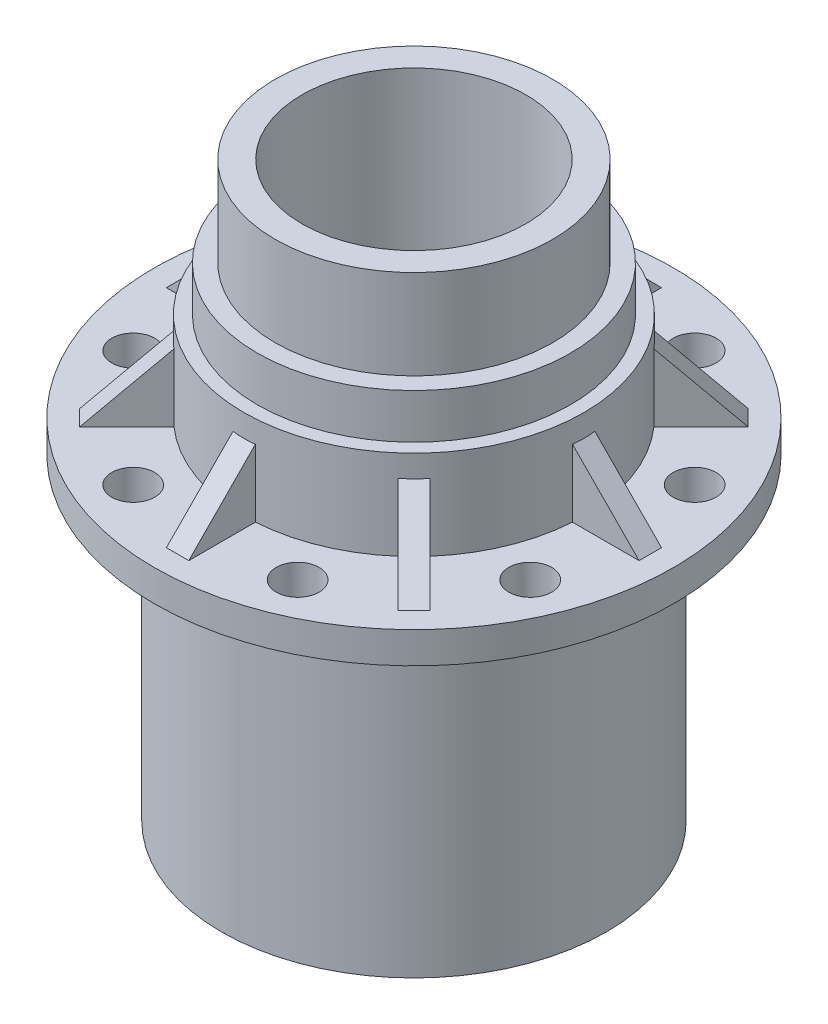
SolidWorks part; units mm, degrees
material "Plain Carbon Steel"
ref_plane "Front Plane" through (0, 0, 0) normal (0, 0, 1) x (1, 0, 0)
ref_plane "Top Plane" through (0, 0, 0) normal (0, 1, 0) x (1, 0, 0)
ref_plane "Right Plane" through (0, 0, 0) normal (1, 0, 0) x (0, 0, -1)
sketch "Sketch1" plane through (0, 0, 0) normal (0, 0, 1) x (1, 0, 0)
  line L0 (0, 580.7528) -> (0, -580.7528) construction
  line L1 (125, 640) -> (125, 390)
  line L6 (125, 390) -> (80, 390)
  line L7 (80, 390) -> (80, 355)
  line L8 (80, 355) -> (125, 355)
  line L9 (125, 355) -> (105, 225)
  line L10 (105, 225) -> (80, 225)
  line L11 (80, 225) -> (80, 200)
  line L12 (80, 200) -> (105, 200)
  line L13 (105, 200) -> (105, 75)
  line L14 (105, 75) -> (155, 75)
  line L15 (155, 75) -> (155, 0)
  line L16 (155, 0) -> (215, 0)
  line L17 (215, 0) -> (215, 330)
  line L18 (215, 330) -> (190, 330)
  line L19 (190, 330) -> (190, 355)
  line L20 (190, 355) -> (290, 355)
  line L21 (290, 355) -> (290, 390)
  line L22 (290, 390) -> (190, 390)
  line L24 (190, 390) -> (190, 490)
  line L25 (190, 490) -> (175, 490)
  line L26 (175, 490) -> (175, 540)
  line L27 (175, 540) -> (155, 540)
  line L28 (155, 540) -> (155, 640)
  line L29 (155, 640) -> (125, 640)
  point P4 (0, 0)
  dimension "D1" = 430
  dimension "D2" = 160
  dimension "D3" = 250
  dimension "D6" = 210
  dimension "D7" = 310
  dimension "D8" = 310
  dimension "D9" = 350
  dimension "D10" = 100
  dimension "D11" = 50
  dimension "D12" = 380
  dimension "D17" = 25
  dimension "D18" = 125
  dimension "D19" = 75
  dimension "D20" = 640
  dimension "D21" = 25
  dimension "D22" = 35
  dimension "D23" = 580
  dimension "D24" = 100
revolve "Revolve1" add sketch "Sketch1" angle 360 about L0
sketch "Sketch2" plane through (0, 0, 0) normal (0, 0, 1) x (1, 0, 0)
  line L0 (264, 390) -> (190, 465)
  line L4 (290, 390) -> (-290, 390) construction
  line L5 (190, 390) -> (190, 490) construction
  dimension "D1" = 75
  dimension "D2" = 74
rib "Rib1" sketch "Sketch2" sketch "Sketch2" thickness 25 extrusion direction parallel to sketch draft on no parameters "D1"=25
sketch "Sketch3" plane through (0, 390, 0) normal (0, 1, 0) x (1, 0, 0)
  line L0 (0, 0) -> (221.7311, 91.844) construction
  line L1 (0, 0) -> (344.1854, 0) construction
  circle A0 centre (221.7311, 91.844) radius 24
  dimension "D2" = 48
  dimension "D1" = 22.5
  dimension "D3" = 240
extrude "Cut-Extrude1" cut sketch "Sketch3" against normal up to next (35 mm away)
pattern_circular "CirPattern1" count 8 over 360 about axis through (0, 0, 0) along (0, 1, 0) of "Rib1"
pattern_circular "CirPattern2" count 8 over 360 about axis through (0, 0, 0) along (0, 1, 0) of "Cut-Extrude1"
